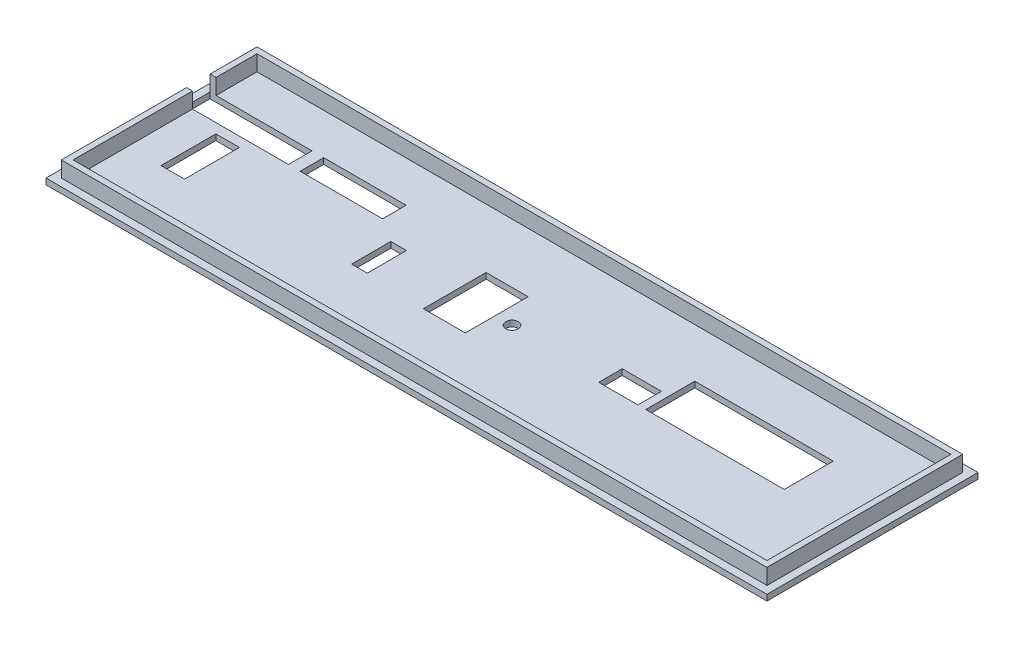
SolidWorks part; units mm, degrees
ref_plane "前视基准面" through (0, 0, 0) normal (0, 0, 1) x (1, 0, 0)
ref_plane "上视基准面" through (0, 0, 0) normal (0, 1, 0) x (1, 0, 0)
ref_plane "右视基准面" through (0, 0, 0) normal (1, 0, 0) x (0, 0, -1)
sketch "草图1" plane through (0, 0, 0) normal (0, 1, 0) x (1, 0, 0)
  line L0 (91.9, 26.9) -> (-91.9, 26.9)
  line L1 (90, -25) -> (-90, -25) construction
  line L2 (90, -25) -> (90, 25) construction
  line L3 (90, 25) -> (-90, 25) construction
  line L4 (-90, -25) -> (-90, 25) construction
  line L5 (90, -25) -> (-90, 25) construction
  line L6 (90, 25) -> (-90, -25) construction
  line L7 (-91.9, -26.9) -> (-91.9, 26.9)
  line L8 (91.9, -26.9) -> (-91.9, -26.9)
  line L9 (91.9, -26.9) -> (91.9, 26.9)
  line L10 (89.95, 24.95) -> (-89.95, 24.95) construction
  line L11 (-89.95, -24.95) -> (-89.95, 24.95) construction
  line L12 (89.95, -24.95) -> (-89.95, -24.95) construction
  line L13 (89.95, -24.95) -> (89.95, 24.95) construction
  point P0 (0, 0)
  dimension "D1" = 180
  dimension "D2" = 50
  dimension "D3" = 1.9
  dimension "D4" = 1.95
extrude "凸台-拉伸1" add sketch "草图1" along normal blind 1.5
sketch "草图2" plane through (0, 1.5, 0) normal (0, 1, 0) x (1, 0, 0)
  line L0 (89.95, -24.95) -> (-89.95, -24.95) construction
  line L1 (89.95, -24.95) -> (89.95, 24.95) construction
  line L2 (-89.95, -24.95) -> (-89.95, 24.95) construction
  line L3 (89.95, 24.95) -> (-89.95, 24.95) construction
  line L4 (89.95, 24.95) -> (-89.95, 24.95)
  line L5 (-89.95, -24.95) -> (-89.95, 24.95)
  line L6 (89.95, -24.95) -> (89.95, 24.95)
  line L7 (89.95, -24.95) -> (-89.95, -24.95)
  line L8 (88.45, 23.45) -> (-88.45, 23.45)
  line L9 (-88.45, -23.45) -> (-88.45, 23.45)
  line L10 (88.45, -23.45) -> (-88.45, -23.45)
  line L11 (88.45, -23.45) -> (88.45, 23.45)
  dimension "D1" = 1.5
extrude "凸台-拉伸2" add sketch "草图2" along normal blind 4
sketch "草图3" plane through (0, 0, 0) normal (0, -1, 0) x (1, 0, 0)
  line L1 (90, -25) -> (-90, -25) construction
  line L2 (-64, -13) -> (-90, -13)
  line L3 (-64, -13) -> (-64, -7)
  line L4 (-64, -7) -> (-90, -7)
  line L5 (-89.95, 24.95) -> (-89.95, -24.95) construction
  line L6 (-90, 25) -> (-90, -25) construction
  line L7 (-61, -13) -> (-40, -13)
  line L8 (-61, -13) -> (-61, -7)
  line L9 (-61, -7) -> (-40, -7)
  line L10 (-40, -13) -> (-40, -7)
  line L11 (89.95, -24.95) -> (-89.95, -24.95) construction
  line L12 (89.95, 24.95) -> (-89.95, 24.95) construction
  line L13 (-4.25, -8.35) -> (-14.95, -8.35)
  line L14 (-4.25, -8.35) -> (-4.25, 7.65)
  line L15 (-4.25, 7.65) -> (-14.95, 7.65)
  line L16 (-14.95, -8.35) -> (-14.95, 7.65)
  line L17 (89.95, 24.95) -> (89.95, -24.95) construction
  line L18 (70.95, -10.95) -> (35.65, -10.95)
  line L19 (70.95, -10.95) -> (70.95, 1.55)
  line L20 (70.95, 1.55) -> (35.65, 1.55)
  line L21 (35.65, -10.95) -> (35.65, 1.55)
  line L22 (-33.95, 6.95) -> (-29.95, 6.95)
  line L23 (-33.95, 6.95) -> (-33.95, -3.05)
  line L24 (-33.95, -3.05) -> (-29.95, -3.05)
  line L25 (-29.95, 6.95) -> (-29.95, -3.05)
  line L26 (-90, -13) -> (-90, -7)
  line L27 (-64, -13) -> (-90, -7) construction
  line L28 (-64, -7) -> (-90, -13) construction
  line L29 (90, 25) -> (-90, 25) construction
  line L30 (33.65, -4.45) -> (23.65, -4.45)
  line L31 (33.65, -4.45) -> (33.65, 1.55)
  line L32 (33.65, 1.55) -> (23.65, 1.55)
  line L33 (23.65, -4.45) -> (23.65, 1.55)
  line L34 (33.65, -4.45) -> (23.65, 1.55) construction
  line L35 (33.65, 1.55) -> (23.65, -4.45) construction
  line L36 (-80, 9.5) -> (-74, 9.5)
  line L37 (-80, 9.5) -> (-80, -4.5)
  line L38 (-80, -4.5) -> (-74, -4.5)
  line L39 (-74, 9.5) -> (-74, -4.5)
  line L40 (-80, 9.5) -> (-74, -4.5) construction
  line L41 (-80, -4.5) -> (-74, 9.5) construction
  circle A0 centre (0, 0) radius 1.6
  point P2 (-77, -10)
  point P22 (-9.6, 7.65)
  point P33 (-31.95, 6.95)
  point P37 (28.65, -1.45)
  point P42 (-77, 2.5)
  dimension "D3" = 0
  dimension "D4" = 26
  dimension "D5" = 29
  dimension "D6" = 6
  dimension "D7" = 21
  dimension "D8" = 12
  dimension "D9" = 16
  dimension "D10" = 10.7
  dimension "D11" = 17.3
  dimension "D12" = 75
  dimension "D13" = 35.3
  dimension "D14" = 12.5
  dimension "D15" = 14
  dimension "D16" = 15
  dimension "D17" = 4
  dimension "D18" = 10
  dimension "D19" = 18
  dimension "D20" = 19
  dimension "D21" = 6
  dimension "D22" = 12
  dimension "D23" = 6
  dimension "D24" = 2
  dimension "D25" = 10
  dimension "D26" = 0
  dimension "D27" = 14
  dimension "D28" = 6
  dimension "D29" = 15.5
  dimension "D30" = 16
extrude "切除-拉伸1" cut sketch "草图3" against normal blind 10
